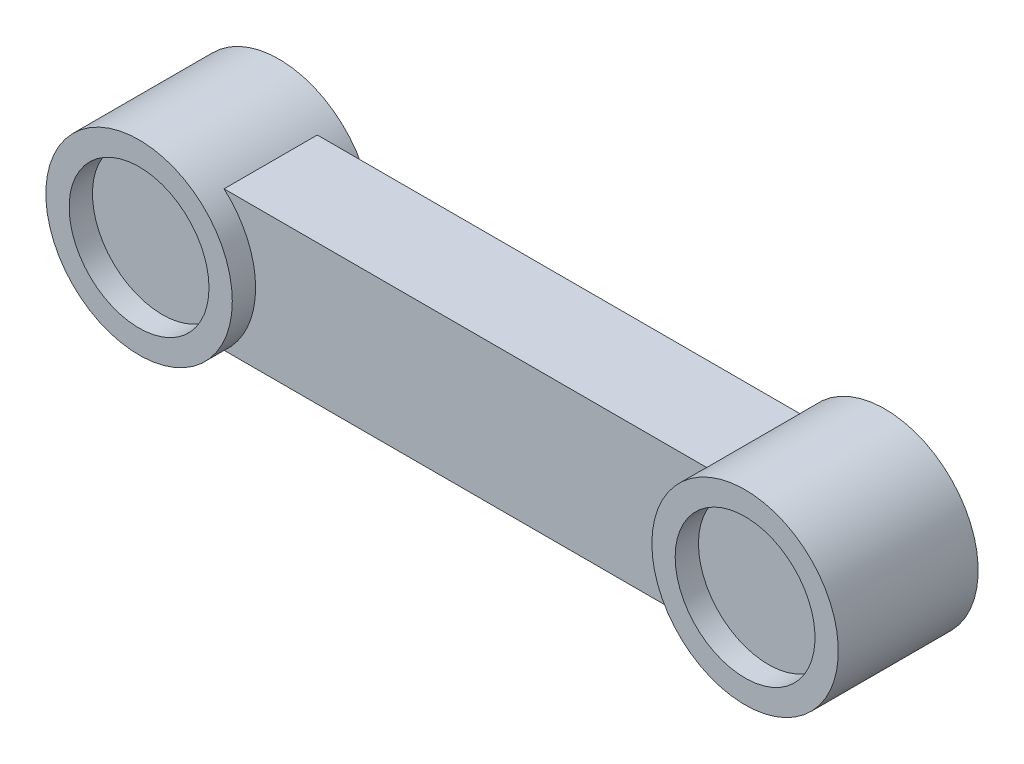
SolidWorks part; units mm, degrees
ref_plane "Front Plane" through (0, 0, 0) normal (0, 0, 1) x (1, 0, 0)
ref_plane "Top Plane" through (0, 0, 0) normal (0, 1, 0) x (1, 0, 0)
ref_plane "Right Plane" through (0, 0, 0) normal (1, 0, 0) x (0, 0, -1)
sketch "Sketch1" plane through (0, 0, 0) normal (0, 0, 1) x (1, 0, 0)
  line L0 (0, 0) -> (260, 0) construction
  line L1 (130, 0) -> (130, 151.8111) construction
  circle A0 centre (0, 0) radius 40
  circle A1 centre (260, 0) radius 40
  dimension "D1" = 80
  dimension "D2" = 260
extrude "Boss-Extrude1" add sketch "Sketch1" along normal blind 60
sketch "Sketch3" plane through (0, 0, 0) normal (0, 0, -1) x (-1, 0, 0)
  circle A0 centre (0, 0) radius 6
  dimension "D1" = 12
sketch "Sketch4" plane through (0, 0, 0) normal (0, 0, -1) x (-1, 0, 0)
  line L0 (-220, 0) -> (-260, 0) construction
  circle A0 centre (-260, 0) radius 40 construction
  circle A1 centre (-260, 0) radius 6
  dimension "D1" = 12
sketch3d "3DSketch1"
  point P0 (-39.9055, -2.7479, 29.8675)
ref_plane "Plane1" through (230.0945, 0, 0) normal (-1, 0, 0) x (0, 0, 1)
sketch "Sketch5" plane through (230.0945, 0, 0) normal (-1, 0, 0) x (0, 0, 1)
  line L0 (60, 0) -> (30, 0) construction
  line L1 (60, -40) -> (60, 40) construction
  line L3 (10, 30) -> (50, 30)
  line L4 (10, 30) -> (10, -30)
  line L5 (10, -30) -> (50, -30)
  line L6 (50, 30) -> (50, -30)
  line L7 (10, 30) -> (50, -30) construction
  line L8 (10, -30) -> (50, 30) construction
  dimension "D1" = 30
  dimension "D2" = 60
  dimension "D3" = 40
extrude "Boss-Extrude3" add sketch "Sketch5" against normal up to surface and the other way up to surface
sketch "Sketch6" plane through (0, 0, 60) normal (0, 0, 1) x (1, 0, 0)
  line L0 (260, -40) -> (260, 0) construction
  line L1 (0, 0) -> (260, 0) construction
  line L2 (130, 0) -> (130, 137.0474) construction
  circle A0 centre (0, 0) radius 30
  circle A1 centre (260, 0) radius 40 construction
  circle A2 centre (260, 0) radius 30
  dimension "D1" = 60
extrude "Cut-Extrude3" cut sketch "Sketch3" against normal blind 10
extrude "Boss-Extrude4" add sketch "Sketch4" along normal blind 10
extrude "Cut-Extrude4" cut sketch "Sketch6" against normal blind 10
